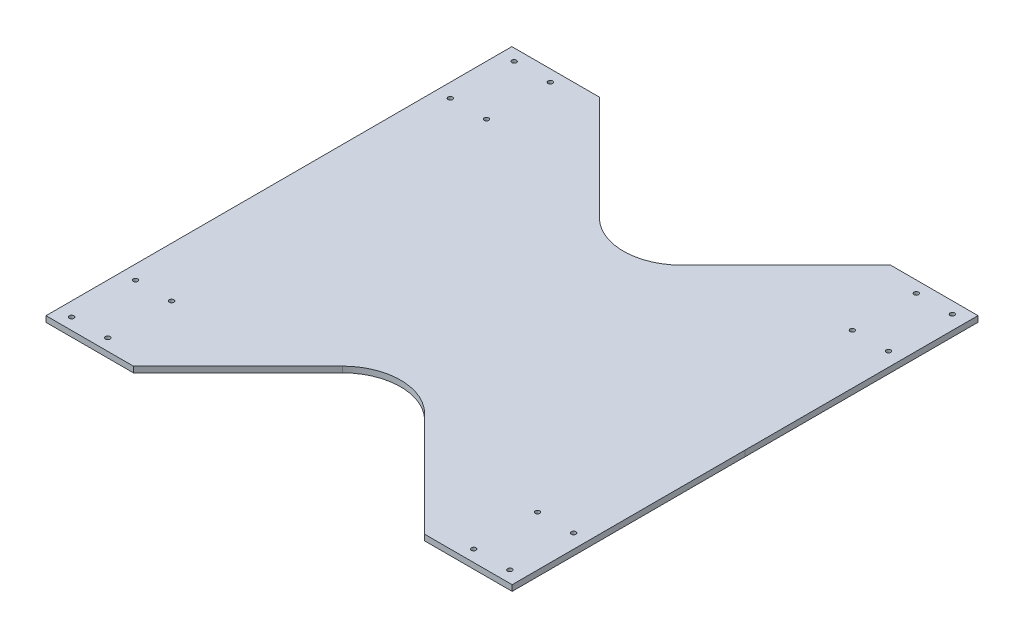
SolidWorks part; units mm, degrees
ref_plane "Front Plane" through (0, 0, 0) normal (0, 0, 1) x (1, 0, 0)
ref_plane "Top Plane" through (0, 0, 0) normal (0, 1, 0) x (1, 0, 0)
ref_plane "Right Plane" through (0, 0, 0) normal (1, 0, 0) x (0, 0, -1)
sketch "Sketch1" plane through (0, 0, 0) normal (0, 1, 0) x (1, 0, 0)
  line L0 (-171.3851, 78.7194) -> (-46.3851, 203.7655)
  line L1 (-46.3851, 203.7655) -> (28.6149, 203.7655)
  line L2 (28.6149, 203.7655) -> (28.6149, 3.7655)
  line L7 (28.7071, -196.2345) -> (28.6149, 3.7655)
  line L8 (-46.2929, -196.2691) -> (28.7071, -196.2345)
  line L9 (-171.3505, -71.2806) -> (-46.2929, -196.2691)
  line L10 (-171.3851, 78.7194) -> (-171.3505, -71.2806) construction
  line L11 (-171.3505, -71.2806) -> (-296.3505, -196.3267)
  line L12 (-171.3851, 78.7194) -> (-296.4428, 203.7078)
  line L13 (-296.3505, -196.3267) -> (-371.3505, -196.3267)
  line L14 (-371.3505, -196.3267) -> (-371.3505, 3.6733)
  line L15 (-371.4427, 203.6732) -> (-371.3505, 3.6733)
  line L16 (-296.4428, 203.7078) -> (-371.4427, 203.6732)
  circle A0 centre (16.6149, 193.7655) radius 1.95
  circle A1 centre (-14.3851, 193.7655) radius 1.95
  circle A2 centre (-14.3851, 138.9255) radius 1.95
  circle A3 centre (16.6149, 138.9255) radius 1.95
  circle A4 centre (16.6772, -131.4) radius 1.95
  circle A5 centre (-14.3228, -131.4143) radius 1.95
  circle A6 centre (16.7025, -186.24) radius 1.95
  circle A7 centre (-14.2975, -186.2543) radius 1.95
  circle A8 centre (-328.3505, -186.3267) radius 1.95
  circle A9 centre (-359.3505, -186.3267) radius 1.95
  circle A10 centre (-328.3505, -131.4867) radius 1.95
  circle A11 centre (-359.3505, -131.4867) radius 1.95
  circle A12 centre (-359.4128, 138.8388) radius 1.95
  circle A13 centre (-328.4128, 138.8531) radius 1.95
  circle A14 centre (-328.4381, 193.6931) radius 1.95
  circle A15 centre (-359.4381, 193.6788) radius 1.95
  point P44 (0, 0)
  dimension "D4" = 3.9
  dimension "D6" = 3.9
  dimension "D7" = 3.9
  dimension "D8" = 3.9
  dimension "D9" = 10
  dimension "D10" = 10
  dimension "D11" = 54.84
  dimension "D12" = 54.84
  dimension "D13" = 31
  dimension "D14" = 12
  dimension "D15" = 12
  dimension "D16" = 31
  dimension "D1" = 200
  dimension "D3" = 75
extrude "Boss-Extrude1" add sketch "Sketch1" along normal blind 5
fillet "Fillet1" radius 50 2 edges at (-171.3851, 2.5, -78.7194) (-171.3505, 2.5, 71.2806)
